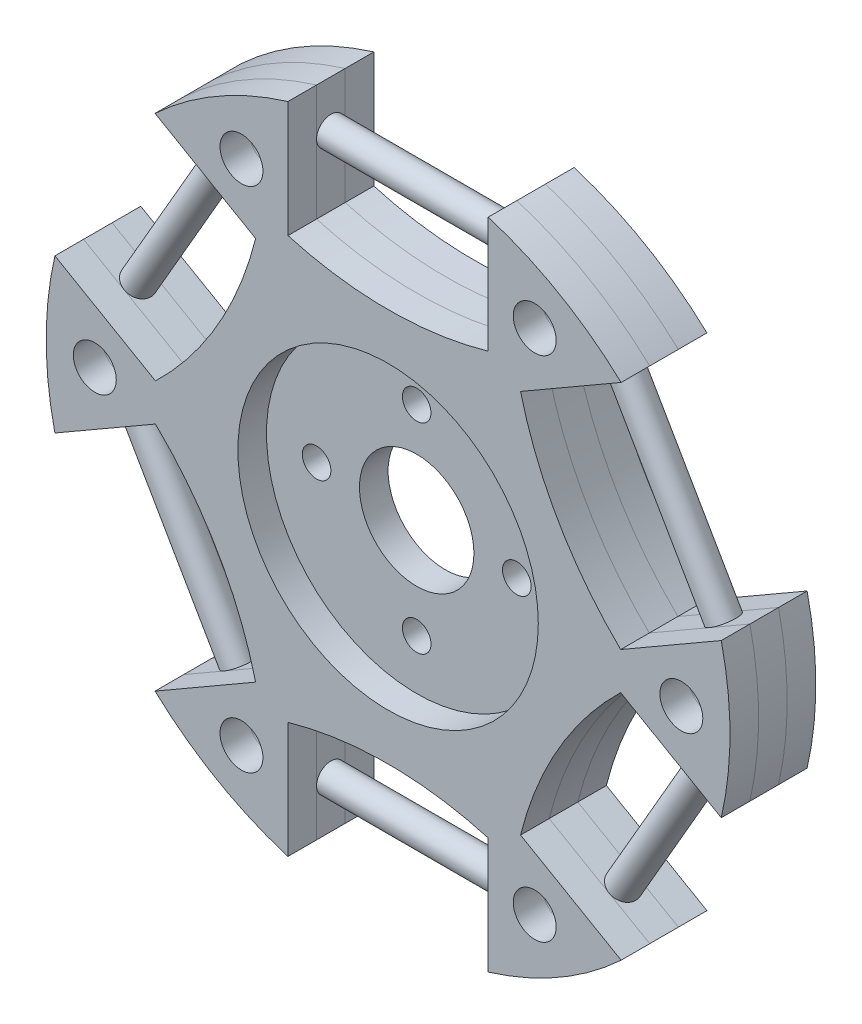
SolidWorks part; units mm, degrees
material "1023 碳钢板 (SS)"
ref_plane "前视基准面" through (0, 0, 0) normal (0, 0, 1) x (1, 0, 0)
ref_plane "上视基准面" through (0, 0, 0) normal (0, 1, 0) x (1, 0, 0)
ref_plane "右视基准面" through (0, 0, 0) normal (1, 0, 0) x (0, 0, -1)
sketch "草图1" plane through (0, 0, 0) normal (0, 0, 1) x (1, 0, 0)
  circle A0 centre (0, 0) radius 25.4
  circle A1 centre (0, 0) radius 10.5
  dimension "D1" = 50.8
  dimension "D2" = 21
extrude "凸台-拉伸1" add sketch "草图1" along normal blind 2
sketch "草图2" plane through (0, 0, 2) normal (0, 0, 1) x (1, 0, 0)
  circle A0 centre (0, 0) radius 25.4
  circle A1 centre (0, 0) radius 4
  dimension "D1" = 8
extrude "凸台-拉伸2" add sketch "草图2" along normal blind 2 separate body
sketch "草图3" plane through (0, 0, 4) normal (0, 0, 1) x (1, 0, 0)
  circle A0 centre (0, 0) radius 25.4
  circle A1 centre (0, 0) radius 10.5
  dimension "D1" = 21
extrude "凸台-拉伸3" add sketch "草图3" along normal blind 2 separate body
sketch "草图4" plane through (0, 0, 6) normal (0, 0, 1) x (1, 0, 0)
  line L0 (9.2597, 13.429) -> (17.6452, 18.2704)
  line L1 (7, 14.7336) -> (7, 24.4164)
  line L2 (-7, 14.7336) -> (-7, 24.4164)
  line L3 (16.2597, 1.3046) -> (24.6452, 6.146)
  line L4 (16.2597, -1.3046) -> (24.6452, -6.146)
  line L5 (9.2597, -13.429) -> (17.6452, -18.2704)
  line L6 (7, -14.7336) -> (7, -24.4164)
  line L7 (-7, -14.7336) -> (-7, -24.4164)
  line L8 (-9.2597, -13.429) -> (-17.6452, -18.2704)
  line L9 (-16.2597, -1.3046) -> (-24.6452, -6.146)
  line L10 (-16.2597, 1.3046) -> (-24.6452, 6.146)
  line L11 (-9.2597, 13.429) -> (-17.6452, 18.2704)
  arc A0 (7, 24.4164) -> (-7, 24.4164) centre (0, 0) ccw
  arc A1 (9.2597, 13.429) -> (16.2597, 1.3046) centre (33.9049, 19.575) ccw
  arc A2 (-7, 14.7336) -> (7, 14.7336) centre (0, 39.15) ccw
  arc A3 (24.6452, 6.146) -> (17.6452, 18.2704) centre (0, 0) ccw
  arc A4 (16.2597, -1.3046) -> (9.2597, -13.429) centre (33.9049, -19.575) ccw
  arc A5 (17.6452, -18.2704) -> (24.6452, -6.146) centre (0, 0) ccw
  arc A6 (7, -14.7336) -> (-7, -14.7336) centre (0, -39.15) ccw
  arc A7 (-7, -24.4164) -> (7, -24.4164) centre (0, 0) ccw
  arc A8 (-9.2597, -13.429) -> (-16.2597, -1.3046) centre (-33.9049, -19.575) ccw
  arc A9 (-24.6452, -6.146) -> (-17.6452, -18.2704) centre (0, 0) ccw
  arc A10 (-16.2597, 1.3046) -> (-9.2597, 13.429) centre (-33.9049, 19.575) ccw
  arc A11 (-17.6452, 18.2704) -> (-24.6452, 6.146) centre (0, 0) ccw
  point P34 (0, 0)
  dimension "D1" = 50.8
  dimension "D2" = 6
  dimension "D3" = 50.8
extrude "切除-拉伸1" cut sketch "草图4" against normal blind 20.5
sketch "草图5" plane through (0, 0, 6) normal (0, 0, 1) x (1, 0, 0)
  circle A0 centre (0, 0) radius 4 construction
  circle A2 centre (10.25, 17.7535) radius 1.5
  circle A3 centre (20.5, 0) radius 1.5
  circle A4 centre (10.25, -17.7535) radius 1.5
  circle A5 centre (-10.25, -17.7535) radius 1.5
  circle A6 centre (-20.5, 0) radius 1.5
  circle A7 centre (-10.25, 17.7535) radius 1.5
  point P21 (0, 0)
  dimension "D1" = 20.5
  dimension "D2" = 3
  dimension "D3" = 6
extrude "切除-拉伸2" cut sketch "草图5" against normal blind 20.5
sketch "草图6" plane through (-7, 0, 0) normal (1, 0, 0) x (0, 0, -1)
  line L0 (-2, 24.4164) -> (-2, 14.7336) construction
  circle A0 centre (-3, 19.575) radius 1
  dimension "D1" = 2
  dimension "D2" = 1
extrude "凸台-拉伸4" add sketch "草图6" along normal blind 14
pattern_circular "阵列(圆周)1" count 6 over 360 about axis through (0, 0, 6) along (0, 0, 1) of "凸台-拉伸4"
sketch "草图7" plane through (0, 0, 4) normal (0, 0, 1) x (1, 0, 0)
  circle A1 centre (-7, 0) radius 1
  circle A2 centre (0, 7) radius 1
  circle A3 centre (7, 0) radius 1
  circle A4 centre (0, -7) radius 1
  point P14 (0, 0)
  dimension "D2" = 2
  dimension "D3" = 4
extrude "切除-拉伸3" cut sketch "草图7" against normal blind 14
sketch "草图8" plane through (0, 0, 6) normal (0, 0, 1) x (1, 0, 0)
  circle A0 centre (0, 0) radius 23.9
  dimension "D1" = 47.8
extrude "切除-拉伸-薄壁1" cut sketch "草图8" against normal blind 10 thin
